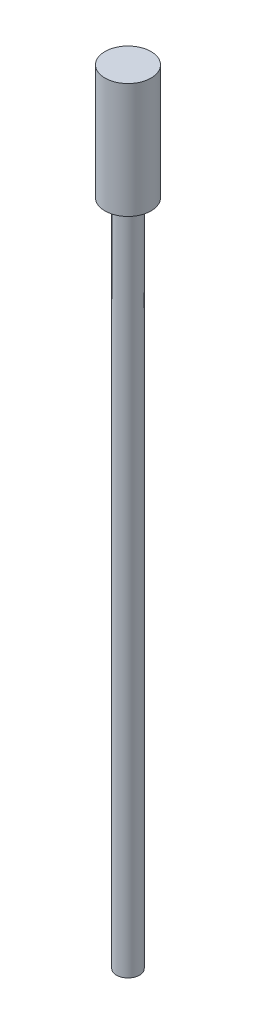
SolidWorks part; units mm, degrees
ref_plane "Front Plane" through (0, 0, 0) normal (0, 0, 1) x (1, 0, 0)
ref_plane "Top Plane" through (0, 0, 0) normal (0, 1, 0) x (1, 0, 0)
ref_plane "Right Plane" through (0, 0, 0) normal (1, 0, 0) x (0, 0, -1)
ref_plane "Plane1" through (0, 0, 0) normal (0, 0, 1) x (1, 0, 0)
sketch "S2D0002" plane through (0, 0, 0) normal (0, 0, 1) x (1, 0, 0)
  line L0 (0.25, 0) -> (0.25, -14.5)
  line L1 (0.25, 0) -> (0.5, 0)
  line L2 (0.5, 0) -> (0.5, 2.5)
  line L3 (0.5, 2.5) -> (0, 2.5)
  line L4 (0, 2.5) -> (0, -14.5)
  line L5 (0, -14.5) -> (0.25, -14.5)
  line L6 (0, 3.35) -> (0, -15.35) construction
revolve "Revolve1" add sketch "S2D0002" angle 360 about L6
